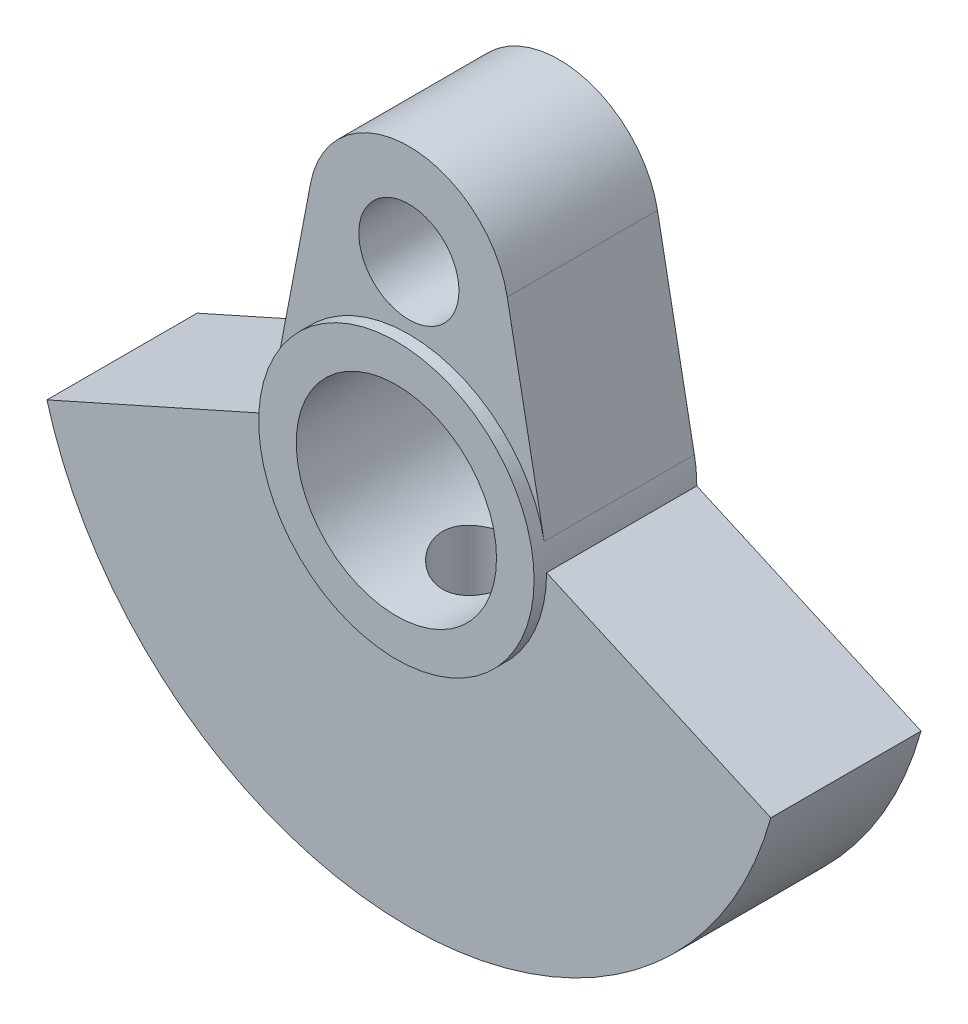
SolidWorks part; units mm, degrees
ref_plane "Front Plane" through (0, 0, 0) normal (0, 0, 1) x (1, 0, 0)
ref_plane "Top Plane" through (0, 0, 0) normal (0, 1, 0) x (1, 0, 0)
ref_plane "Right Plane" through (0, 0, 0) normal (1, 0, 0) x (0, 0, -1)
sketch "Sketch1" plane through (0, 0, 0) normal (0, 0, 1) x (1, 0, 0)
  line L0 (0, 28.5712) -> (0, 4) construction
  line L1 (5.5, 0) -> (-5.5, 0) construction
  line L2 (-5.5, 0) -> (-14.4568, -4)
  line L3 (-3.9291, 8.75) -> (-5.4025, 1.0312)
  line L4 (3.9291, 8.75) -> (5.4025, 1.0312)
  line L5 (0, -5.5) -> (0, -29.831) construction
  line L6 (5.5, 0) -> (14.4568, -4)
  circle A0 centre (0, 8) radius 2
  arc A1 (-14.4568, -4) -> (14.4568, -4) centre (0, 0) ccw
  arc A2 (3.9291, 8.75) -> (-3.9291, 8.75) centre (0, 8) ccw
  arc A3 (-5.4025, 1.0312) -> (-5.5, 0) centre (0, 0) ccw
  arc A4 (5.5, 0) -> (5.4025, 1.0312) centre (0, 0) ccw
  dimension "D1" = 30
  dimension "D2" = 4
  dimension "D3" = 8
  dimension "D5" = 11
  dimension "D4" = 8
  dimension "D6" = 4
extrude "Boss-Extrude1" add sketch "Sketch1" along normal mid plane 6
sketch "Sketch2" plane through (0, 0, 3) normal (0, 0, 1) x (1, 0, 0)
  circle A0 centre (0, 0) radius 5.5
  circle A1 centre (0, 0) radius 4
  dimension "D1" = 11
  dimension "D2" = 8
extrude "Boss-Extrude2" add sketch "Sketch2" along normal blind 0.5
sketch "Sketch4" plane through (0, 0, 3) normal (0, 0, 1) x (1, 0, 0)
  circle A1 centre (0, 0) radius 4
  circle A2 centre (0, 0) radius 4
  dimension "D1" = 0
extrude "Cut-Extrude2" cut sketch "Sketch4" against normal through all
hole_wizard "M4 Tapped Hole1" positions "Sketch6" profile "Sketch8" tap size "M4" standard "ISO"
sketch "Sketch6" plane through (0, 0, 0) normal (0, 1, 0) x (1, 0, 0)
  point P0 (0, 0)
sketch "Sketch8" plane through (0, 0, 0) normal (1, 0, 0) x (0, 0, 1)
  line L0 (0, 0) -> (0, 22.4914)
  line L1 (0, 22.4914) -> (1.65, 21.5)
  line L2 (1.65, 21.5) -> (1.65, 0)
  line L5 (1.65, 0) -> (0, 0)
  line L10 (0, 22.4914) -> (-1.65, 21.5) construction
  line L11 (0, -6.35) -> (0, 107.95) construction
  dimension "Tap Drill Dia." = 3.3
  dimension "Tap Drill Depth" = 21.5
  dimension "Drill Angle" = 118
